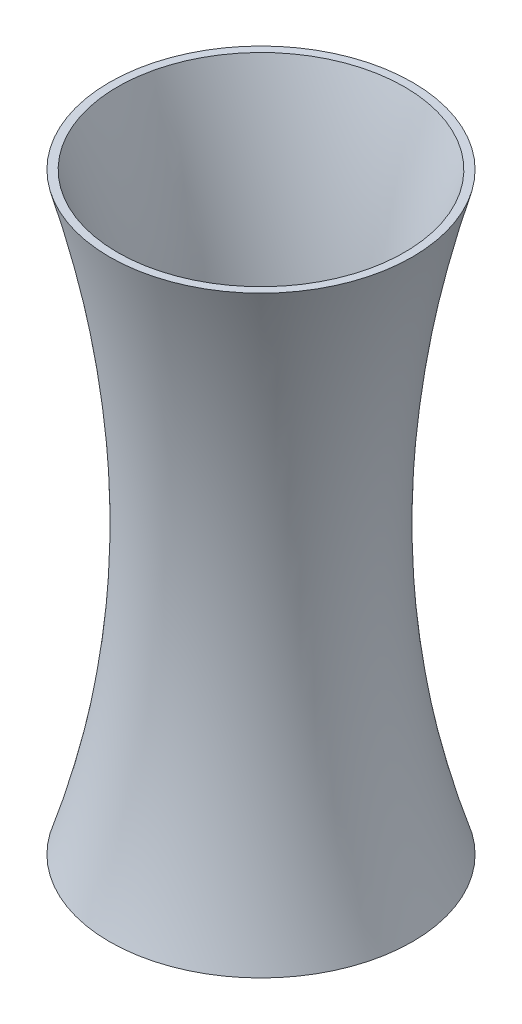
SolidWorks part; units mm, degrees
ref_plane "Front Plane" through (0, 0, 0) normal (0, 0, 1) x (1, 0, 0)
ref_plane "Top Plane" through (0, 0, 0) normal (0, 1, 0) x (1, 0, 0)
ref_plane "Right Plane" through (0, 0, 0) normal (1, 0, 0) x (0, 0, -1)
sketch "Sketch1" plane through (0, 0, 0) normal (0, 0, 1) x (1, 0, 0)
  line L0 (0, 0) -> (0, 190) construction
  line L1 (0, 190) -> (-48.5, 190)
  line L2 (-48.5, 190) -> (-19.925, 88.9) construction
  line L3 (-19.925, 88.9) -> (-48.5, 0) construction
  line L4 (-48.5, 0) -> (0, 0)
  line L5 (-48.5, 190) -> (-45.96, 190)
  line L6 (-48.5, 0) -> (-45.96, 0)
  line L7 (-45.96, 190) -> (-17.385, 101.1) construction
  line L8 (-17.385, 101.1) -> (-45.96, 0) construction
  line L9 (-48.5, 0) -> (-45.96, 0)
  spline S0 degree 2 poles (-48.5, 190) (-19.925, 88.9) (-48.5, 0) knots 0 0 0 1 1 1
  spline S1 degree 2 poles (-45.96, 190) (-17.385, 101.1) (-45.96, 0) knots 0 0 0 1 1 1
  dimension "D3" = 190
  dimension "D1" = 48.5
  dimension "D2" = 48.5
  dimension "D4" = 190
  dimension "D5" = 2.54
  dimension "D6" = 88.9
  dimension "D7" = 88.9
  dimension "D8" = 28.575
  dimension "D9" = 28.575
revolve "Revolve2" add sketch "Sketch1" angle 360 about L0
